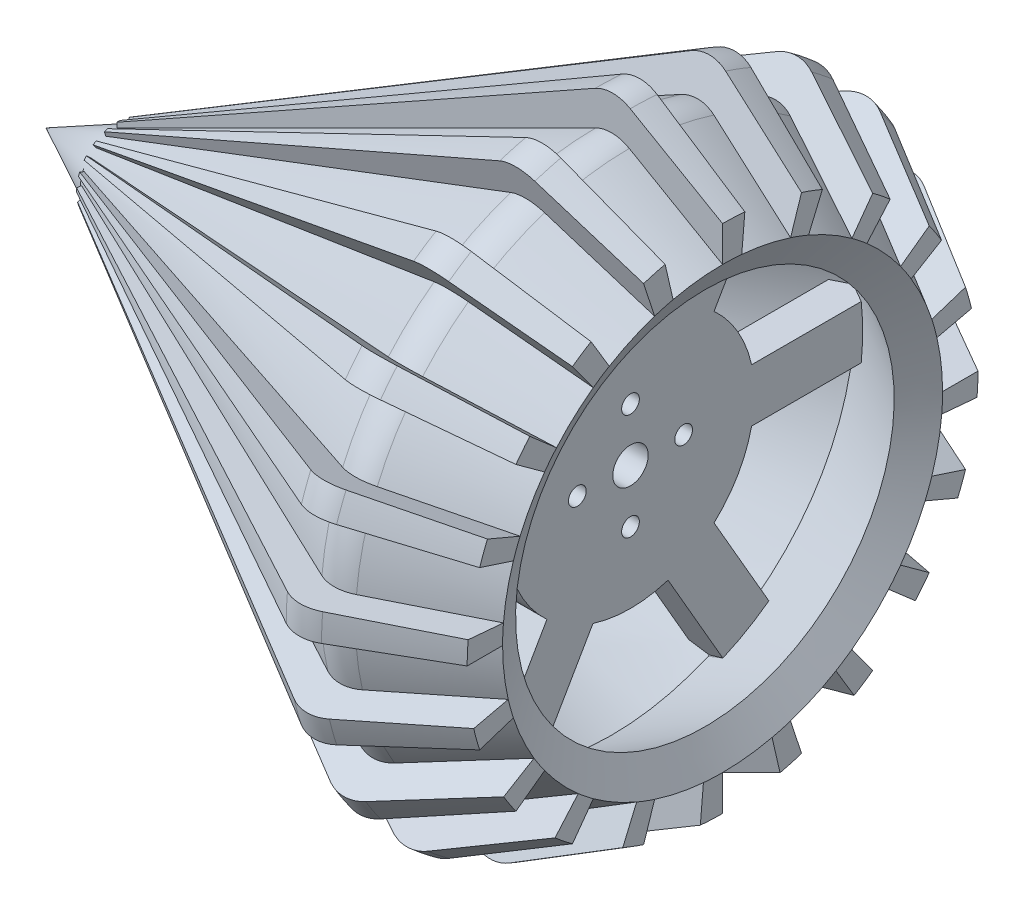
SolidWorks part; units mm, degrees
ref_plane "Front Plane" through (0, 0, 0) normal (0, 0, 1) x (1, 0, 0)
ref_plane "Top Plane" through (0, 0, 0) normal (0, 1, 0) x (1, 0, 0)
ref_plane "Right Plane" through (0, 0, 0) normal (1, 0, 0) x (0, 0, -1)
sketch "Sketch2" plane through (0, 0, 0) normal (0, 0, 1) x (1, 0, 0)
  line L0 (33.4615, 0) -> (-190.5, 0) construction
  line L1 (-190.5, 0) -> (-263.4708, 0) construction
  line L5 (39.3699, 78.8698) -> (0, 101.6)
  line L6 (0, 101.6) -> (-203.2, 0)
  line L8 (33.0199, 67.8713) -> (-0.4322, 87.1849)
  line L9 (-0.4322, 87.1849) -> (-174.8019, 0)
  line L10 (-203.2, 0) -> (-174.8019, 0)
  line L11 (-0.4322, 87.1849) -> (-197.5204, -11.3592) construction
  line L12 (39.3699, 78.8698) -> (33.0199, 67.8713)
  line L13 (0, 0) -> (0, 134.0479) construction
  dimension "D1" = 101.6
  dimension "D2" = 203.2
  dimension "D3" = 12.7
  dimension "D4" = 30
revolve "Revolve1" add sketch "Sketch2" angle 360 about L0
sketch "Sketch3" plane through (0, 0, 0) normal (0, 0, 1) x (1, 0, 0)
  line L0 (-177.8, 14.4619) -> (0, 114.3)
  line L1 (0, 114.3) -> (39.3699, 91.5698)
  line L2 (39.3699, 91.5698) -> (39.3699, 78.8698)
  line L3 (39.3699, 78.8698) -> (0, 101.6)
  line L4 (0, 101.6) -> (-177.8, 12.7)
  line L5 (0, 0) -> (0, 133.0618) construction
  line L6 (95.9453, 0) -> (-261.7553, 0) construction
  line L7 (-177.8, 14.4619) -> (-177.8, 12.7)
  line L8 (0, 101.6) -> (-203.2, 0) construction
  dimension "D1" = 114.3
  dimension "D2" = 177.8
  dimension "D3" = 2.75
revolve "Revolve8" add sketch "Sketch3" angle 5 about L6
ref_axis "Axis1" through (-279.6403, 0, 0) along (1, 0, 0)
pattern_circular "CirPattern3" count 20 over 360 about axis through (0, 0, 0) along (1, 0, 0) of bodies 102
combine bodies "Combine1" bodies to combine 121 102 103 104 105 101 106 107 108 109 110 111 112 113 114 115 117 116 118 119 120
fillet "Fillet2" radius 12.7 40 edges at (0, 71.1534, 89.4521) (0, 50.0302, 88.4281) (0, 40.0287, 107.0616) (0, 20.2558, 99.5603) (0, 4.9857, 114.1912) (0, -11.5014, 100.9469) (0, -30.5453, 110.143) (0, -42.1328, 92.4521) (0, -63.0864, 95.3131) (0, -68.64, 74.9074) (0, -89.4521, 71.1534) (0, -88.4281, 50.0302) (0, -107.0616, 40.0287) (0, -99.5603, 20.2558) (0, -114.1912, 4.9857) (0, -100.9469, -11.5014) (0, -110.143, -30.5453) (0, -92.4521, -42.1328) (0, -95.3131, -63.0864) (0, -74.9074, -68.64) (0, -71.1534, -89.4521) (0, -50.0302, -88.4281) (0, -40.0287, -107.0616) (0, -20.2558, -99.5603) (0, -4.9857, -114.1912) (0, 11.5014, -100.9469) (0, 30.5453, -110.143) (0, 42.1328, -92.4521) (0, 63.0864, -95.3131) (0, 68.64, -74.9074) (0, 89.4521, -71.1534) (0, 88.4281, -50.0302) (0, 107.0616, -40.0287) (0, 99.5603, -20.2558) (0, 100.9469, 11.5014) (0, 92.4521, 42.1328) (0, 74.9074, 68.64) (0, 95.3131, 63.0864) (0, 110.143, 30.5453) (0, 114.1912, -4.9857)
sketch "Sketch4" plane through (0, 0, 0) normal (1, 0, 0) x (0, 0, -1)
  line L0 (0, 55.155) -> (0, -59.58) construction
  line L1 (29.9576, -32.8381) -> (55.8739, -77.7264)
  line L2 (-57.8416, 0) -> (54.3648, 0) construction
  line L3 (43.4175, 9.525) -> (95.25, 9.525)
  line L5 (43.4175, -9.525) -> (95.25, -9.525)
  line L6 (95.25, 9.525) -> (95.25, -9.525)
  line L7 (13.4598, -42.3631) -> (39.3761, -87.2514)
  line L8 (55.8739, -77.7264) -> (39.3761, -87.2514)
  line L9 (-13.4598, -42.3631) -> (-39.3761, -87.2514)
  line L10 (-29.9576, -32.8381) -> (-55.8739, -77.7264)
  line L11 (-39.3761, -87.2514) -> (-55.8739, -77.7264)
  line L12 (-43.4175, -9.525) -> (-95.25, -9.525)
  line L13 (-43.4175, 9.525) -> (-95.25, 9.525)
  line L14 (-95.25, -9.525) -> (-95.25, 9.525)
  line L15 (-29.9576, 32.8381) -> (-55.8739, 77.7264)
  line L16 (-13.4598, 42.3631) -> (-39.3761, 87.2514)
  line L17 (-55.8739, 77.7264) -> (-39.3761, 87.2514)
  line L18 (13.4598, 42.3631) -> (39.3761, 87.2514)
  line L19 (29.9576, 32.8381) -> (55.8739, 77.7264)
  line L20 (39.3761, 87.2514) -> (55.8739, 77.7264)
  arc A0 (43.4175, 9.525) -> (29.9576, 32.8381) centre (0, 0) ccw
  circle A1 centre (0, 0) radius 6.35
  circle A2 centre (0, 19.05) radius 3.175
  circle A3 centre (19.05, 0) radius 3.175
  circle A4 centre (0, -19.05) radius 3.175
  circle A5 centre (-19.05, 0) radius 3.175
  arc A6 (13.4598, 42.3631) -> (-13.4598, 42.3631) centre (0, 0) ccw
  arc A7 (-29.9576, 32.8381) -> (-43.4175, 9.525) centre (0, 0) ccw
  arc A8 (-43.4175, -9.525) -> (-29.9576, -32.8381) centre (0, 0) ccw
  arc A9 (-13.4598, -42.3631) -> (13.4598, -42.3631) centre (0, 0) ccw
  arc A10 (29.9576, -32.8381) -> (43.4175, -9.525) centre (0, 0) ccw
  dimension "D1" = 88.9
  dimension "D6" = 6.35
  dimension "D7" = 6.35
  dimension "D8" = 6.35
  dimension "D9" = 6.35
  dimension "D10" = 12.7
  dimension "D2" = 19.05
  dimension "D3" = 19.05
  dimension "D4" = 19.05
  dimension "D5" = 19.05
  dimension "D12" = 9.525
  dimension "D11" = 19.05
  dimension "D13" = 95.25
  dimension "D14" = 6
extrude "Boss-Extrude1" add sketch "Sketch4" along normal mid plane 12.7
ref_plane "Plane1" through (-127, 0, 0) normal (1, 0, 0) x (0, 0, -1)
sketch "Sketch5" plane through (-127, 0, 0) normal (1, 0, 0) x (0, 0, -1)
  line L0 (-38.9608, 0) -> (64.0175, 0) construction
  line L1 (24.5934, 6.35) -> (44.45, 6.35)
  line L3 (24.5934, -6.35) -> (44.45, -6.35)
  line L4 (44.45, 6.35) -> (44.45, -6.35)
  line L5 (17.796, -18.1235) -> (27.7243, -35.3198)
  line L6 (0, -38.5344) -> (0, 35.4192) construction
  line L7 (27.7243, -35.3198) -> (16.7257, -41.6698)
  line L8 (6.7975, -24.4735) -> (16.7257, -41.6698)
  line L9 (-6.7975, -24.4735) -> (-16.7257, -41.6698)
  line L10 (-16.7257, -41.6698) -> (-27.7243, -35.3198)
  line L11 (-17.796, -18.1235) -> (-27.7243, -35.3198)
  line L12 (-24.5934, -6.35) -> (-44.45, -6.35)
  line L13 (-44.45, -6.35) -> (-44.45, 6.35)
  line L14 (-24.5934, 6.35) -> (-44.45, 6.35)
  line L15 (-17.796, 18.1235) -> (-27.7243, 35.3198)
  line L16 (-27.7243, 35.3198) -> (-16.7257, 41.6698)
  line L17 (-6.7975, 24.4735) -> (-16.7257, 41.6698)
  line L18 (6.7975, 24.4735) -> (16.7257, 41.6698)
  line L19 (16.7257, 41.6698) -> (27.7243, 35.3198)
  line L20 (17.796, 18.1235) -> (27.7243, 35.3198)
  arc A0 (24.5934, 6.35) -> (17.796, 18.1235) centre (0, 0) ccw
  circle A1 centre (0, 0) radius 6.35
  arc A2 (6.7975, 24.4735) -> (-6.7975, 24.4735) centre (0, 0) ccw
  arc A3 (-17.796, 18.1235) -> (-24.5934, 6.35) centre (0, 0) ccw
  arc A4 (-24.5934, -6.35) -> (-17.796, -18.1235) centre (0, 0) ccw
  arc A5 (-6.7975, -24.4735) -> (6.7975, -24.4735) centre (0, 0) ccw
  arc A6 (17.796, -18.1235) -> (24.5934, -6.35) centre (0, 0) ccw
  point P33 (0, 0)
  dimension "D1" = 50.8
  dimension "D2" = 12.7
  dimension "D3" = 12.7
  dimension "D4" = 6.35
  dimension "D5" = 19.8566
  dimension "D6" = 6
extrude "Boss-Extrude2" add sketch "Sketch5" along normal mid plane 12.7 separate body
sketch "Sketch6" plane through (0, 0, 0) normal (0, 0, 1) x (1, 0, 0)
  line L0 (-180.0281, 11.586) -> (-92.0527, 53.6678)
  line L1 (-177.8, 12.7) -> (-203.2, 0) construction
  line L2 (-6.3054, 94.9393) -> (-177.8, 12.3962) construction
  line L3 (-92.0527, 53.6678) -> (-98.5511, 67.2532)
  line L4 (-98.5511, 67.2532) -> (-180.0281, 28.2798)
  line L5 (-180.0281, 28.2798) -> (-180.0281, 11.586)
revolve "Cut-Revolve2" cut sketch "Sketch6" angle 360 about axis through (-279.6403, 0, 0) along (1, 0, 0)
equation "\"boltSpacing\"=0.75"
equation "\"D2@Sketch4\"=\"boltSpacing\""
equation "\"D3@Sketch4\"=\"boltSpacing\""
equation "\"D4@Sketch4\"=\"boltSpacing\""
equation "\"D5@Sketch4\"=\"boltSpacing\""
equation "\"boltSizing\"=0.25"
equation "\"D6@Sketch4\"=\"boltSizing\""
equation "\"D7@Sketch4\"=\"boltSizing\""
equation "\"D8@Sketch4\"=\"boltSizing\""
equation "\"D9@Sketch4\"=\"boltSizing\""
equation "\"shaftSizing\"=0.5"
equation "\"D2@Sketch5\"=\"shaftSizing\""
